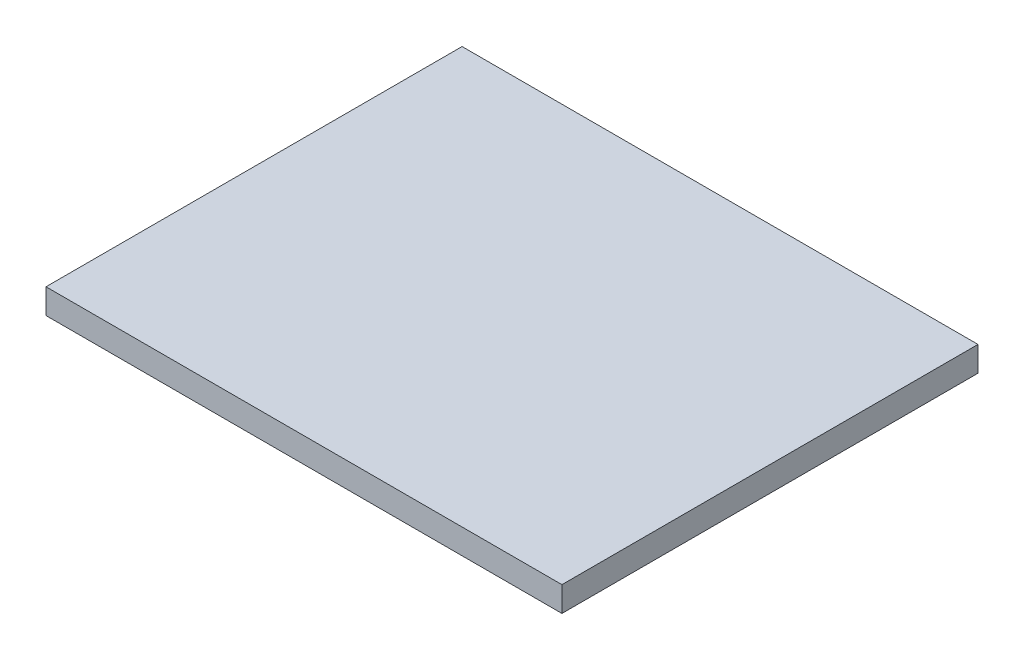
SolidWorks part; units mm, degrees
ref_plane "Plan de face" through (0, 0, 0) normal (0, 0, 1) x (1, 0, 0)
ref_plane "Plan de dessus" through (0, 0, 0) normal (0, 1, 0) x (1, 0, 0)
ref_plane "Plan de droite" through (0, 0, 0) normal (1, 0, 0) x (0, 0, -1)
sketch "Esquisse1" plane through (0, 0, 0) normal (0, 1, 0) x (1, 0, 0)
  line L1 (-155, 125) -> (155, 125)
  line L2 (-155, 125) -> (-155, -125)
  line L3 (-155, -125) -> (155, -125)
  line L4 (155, 125) -> (155, -125)
  line L5 (-155, 125) -> (155, -125) construction
  line L6 (-155, -125) -> (155, 125) construction
  point P0 (0, 0)
  dimension "D1" = 250
  dimension "D2" = 310
extrude "Boss.-Extru.1" add sketch "Esquisse1" along normal blind 15
